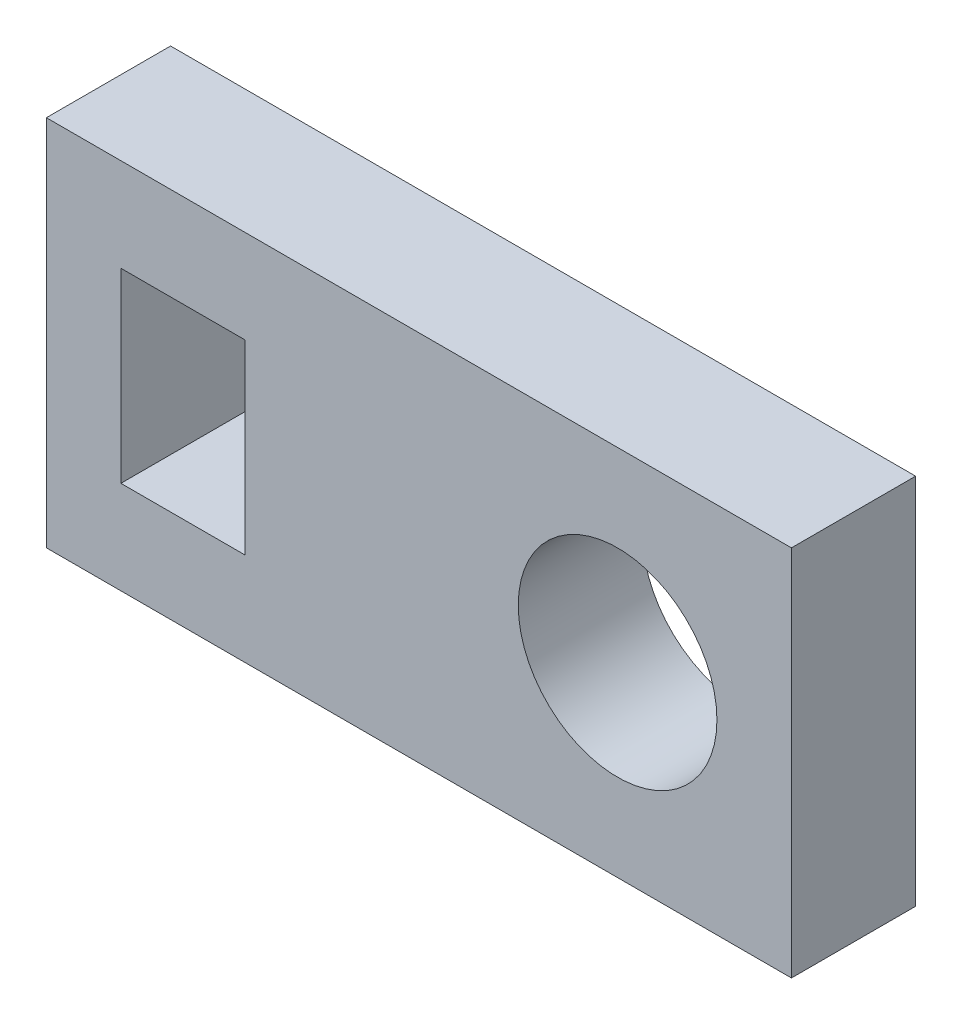
SolidWorks part; units mm, degrees
material "Acrylic (Medium-high impact)"
ref_plane "Front Plane" through (0, 0, 0) normal (0, 0, 1) x (1, 0, 0)
ref_plane "Top Plane" through (0, 0, 0) normal (0, 1, 0) x (1, 0, 0)
ref_plane "Right Plane" through (0, 0, 0) normal (1, 0, 0) x (0, 0, -1)
sketch "Sketch1" plane through (0, 0, 0) normal (0, 0, 1) x (1, 0, 0)
  line L1 (0, 0) -> (30, 0)
  line L2 (0, 0) -> (0, 15)
  line L3 (0, 15) -> (30, 15)
  line L4 (30, 0) -> (30, 15)
  line L5 (3, 11.25) -> (8, 11.25)
  line L6 (3, 11.25) -> (3, 3.75)
  line L7 (3, 3.75) -> (8, 3.75)
  line L8 (8, 11.25) -> (8, 3.75)
  circle A0 centre (23, 7.5) radius 4
  point P8 (0, 7.5)
  point P12 (3, 7.5)
  dimension "D1" = 8
  dimension "D2" = 30
  dimension "D3" = 15
  dimension "D4" = 5
  dimension "D5" = 7.5
  dimension "D6" = 3
  dimension "D7" = 15
extrude "Boss-Extrude1" add sketch "Sketch1" along normal blind 5
